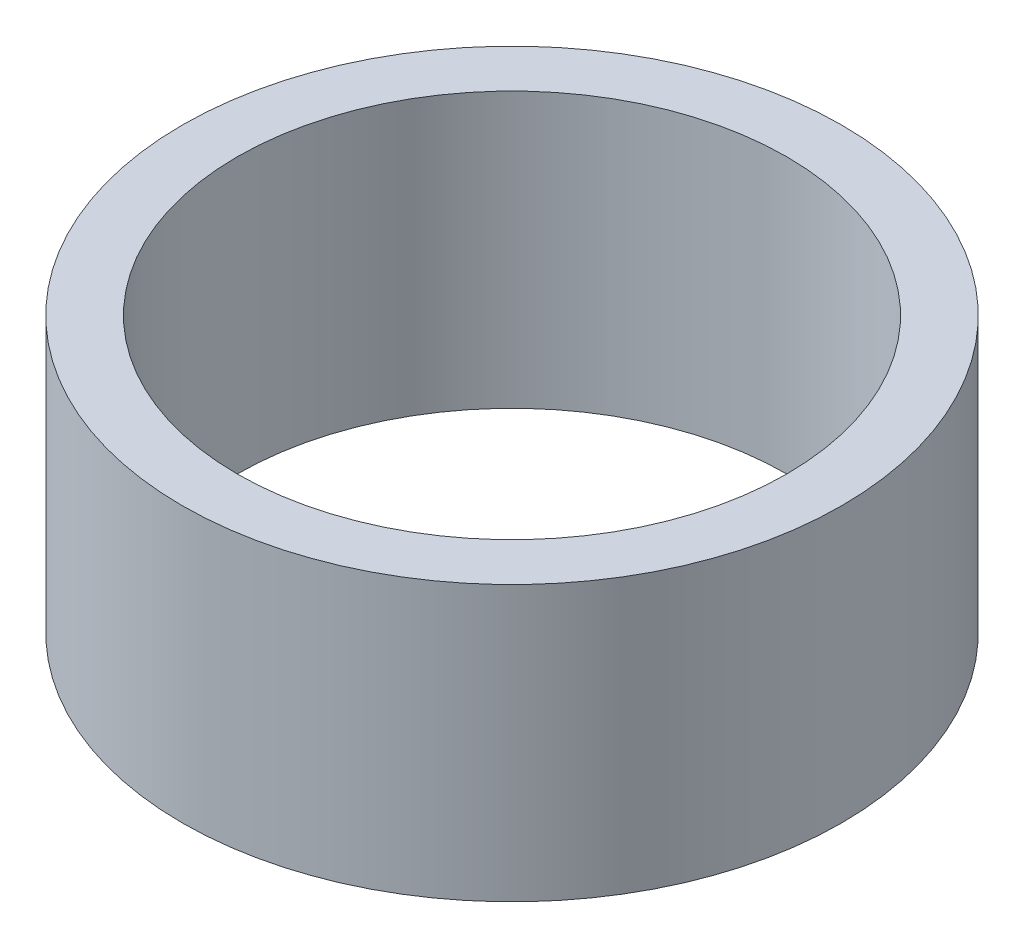
SolidWorks part; units mm, degrees
ref_plane "Front Plane" through (0, 0, 0) normal (0, 0, 1) x (1, 0, 0)
ref_plane "Top Plane" through (0, 0, 0) normal (0, 1, 0) x (1, 0, 0)
ref_plane "Right Plane" through (0, 0, 0) normal (1, 0, 0) x (0, 0, -1)
sketch "Sketch2" plane through (0, 0, 0) normal (0, 1, 0) x (1, 0, 0)
  circle A0 centre (0, 0) radius 30
  circle A1 centre (0, 0) radius 25
  dimension "D1" = 60
  dimension "D2" = 50
extrude "Boss-Extrude1" add sketch "Sketch2" along normal blind 25
